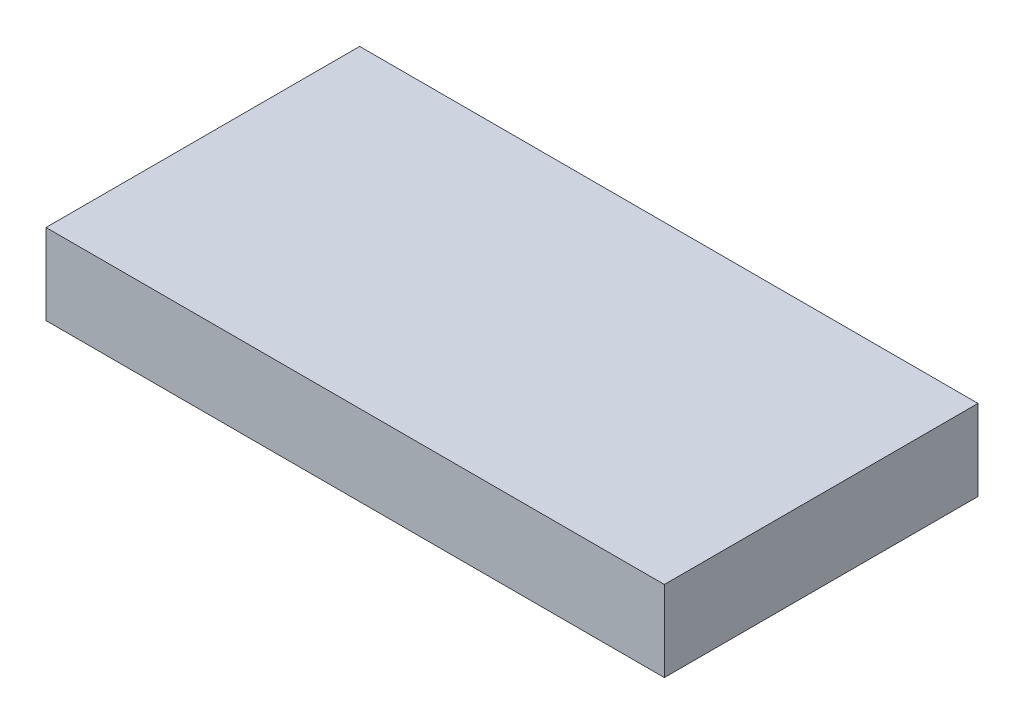
SolidWorks part; units mm, degrees
ref_plane "前视基准面" through (0, 0, 0) normal (0, 0, 1) x (1, 0, 0)
ref_plane "上视基准面" through (0, 0, 0) normal (0, 1, 0) x (1, 0, 0)
ref_plane "右视基准面" through (0, 0, 0) normal (1, 0, 0) x (0, 0, -1)
sketch "草图4" plane through (0, 0, 0) normal (0, 1, 0) x (1, 0, 0)
  line L0 (46.5588, 8.232) -> (40.0533, 8.232) construction
  line L1 (-25.6939, -26.768) -> (43.3061, -26.768)
  line L2 (-25.6939, -26.768) -> (-25.6939, 8.232)
  line L3 (-25.6939, 8.232) -> (43.3061, 8.232)
  line L4 (43.3061, -26.768) -> (43.3061, 8.232)
  dimension "D1" = 69
  dimension "D2" = 35
extrude "凸台-拉伸1" add sketch "草图4" against normal blind 9
